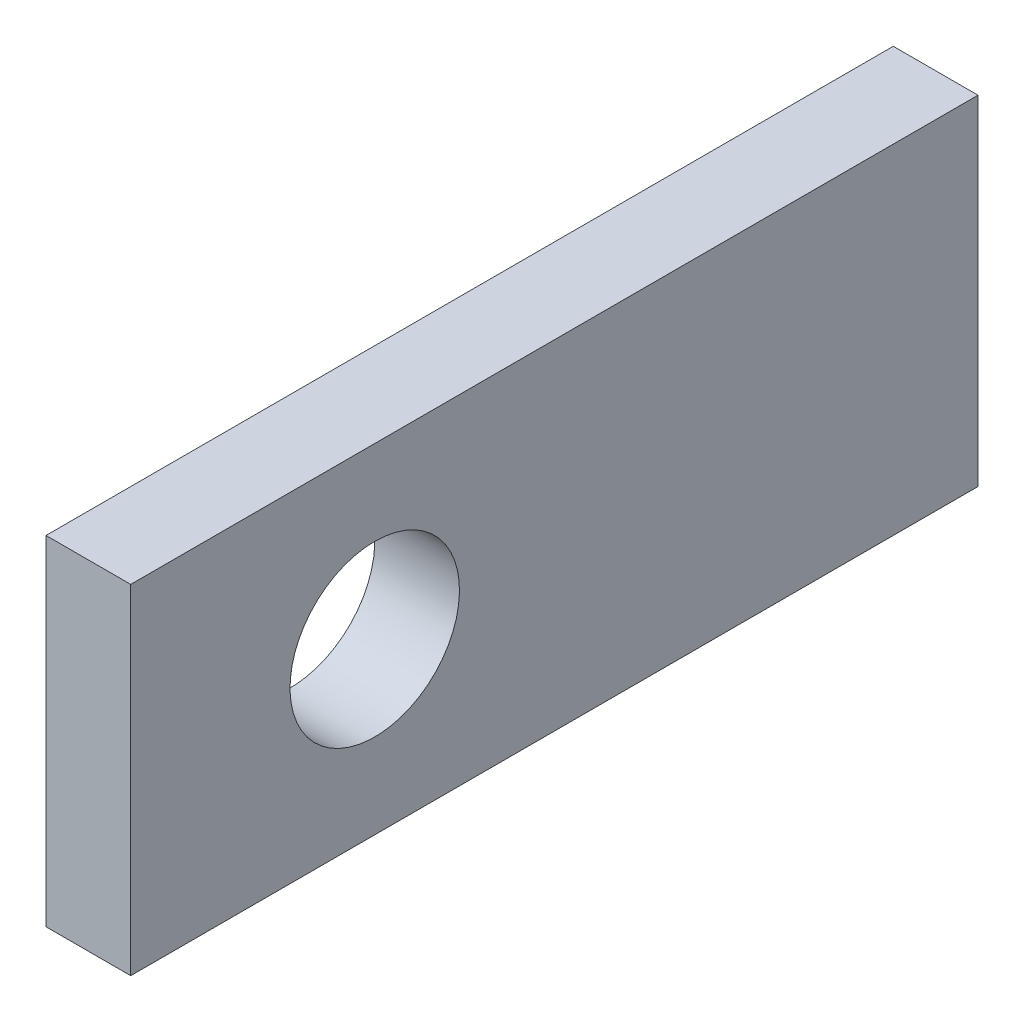
SolidWorks part; units mm, degrees
ref_plane "Front Plane" through (0, 0, 0) normal (0, 0, 1) x (1, 0, 0)
ref_plane "Top Plane" through (0, 0, 0) normal (0, 1, 0) x (1, 0, 0)
ref_plane "Right Plane" through (0, 0, 0) normal (1, 0, 0) x (0, 0, -1)
sketch "Sketch1" plane through (0, 0, 0) normal (0, 0, 1) x (1, 0, 0)
  line L1 (31.9112, 7.5041) -> (35.0862, 7.5041)
  line L2 (31.9112, 7.5041) -> (31.9112, -5.1959)
  line L3 (31.9112, -5.1959) -> (35.0862, -5.1959)
  line L4 (35.0862, 7.5041) -> (35.0862, -5.1959)
  line L5 (35.0862, 14.0855) -> (35.0862, -167.207) construction
  dimension "D1" = 3.175
  dimension "D2" = 12.7
  dimension "D3" = 0
extrude "Boss-Extrude1" add sketch "Sketch1" along normal blind 31.75
sketch "Sketch2" plane through (35.0862, 0, 0) normal (1, 0, 0) x (0, 0, -1)
  line L0 (-31.75, 1.1541) -> (-5.1968, 1.1541) construction
  line L1 (-31.75, -5.1959) -> (-31.75, 7.5041) construction
  circle A0 centre (-22.606, 1.1541) radius 3.175
  dimension "D1" = 6.35
  dimension "D2" = 9.144
extrude "Cut-Extrude1" cut sketch "Sketch2" against normal through all
